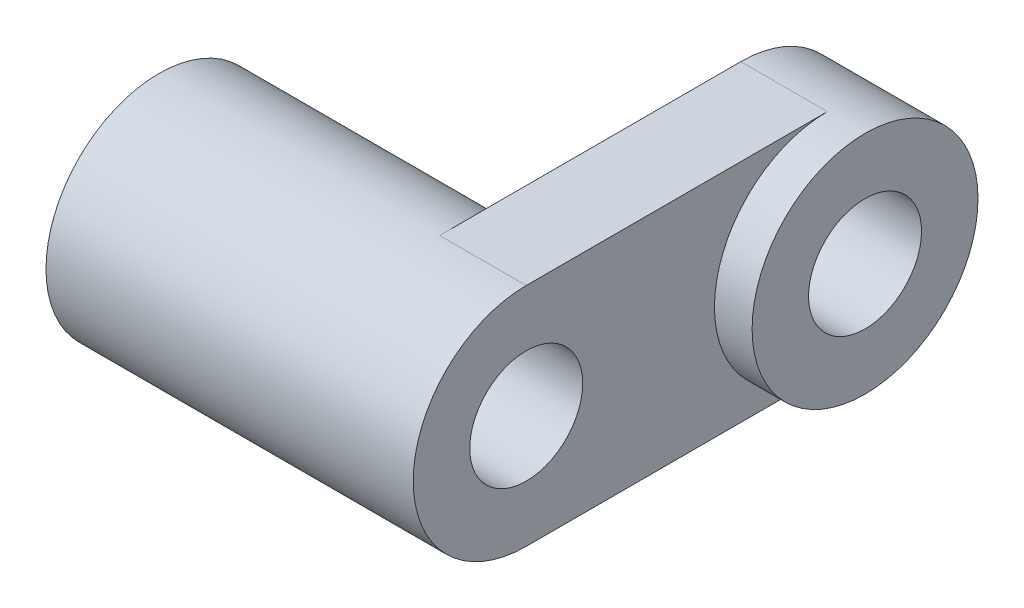
SolidWorks part; units mm, degrees
ref_plane "Front Plane" through (0, 0, 0) normal (0, 0, 1) x (1, 0, 0)
ref_plane "Top Plane" through (0, 0, 0) normal (0, 1, 0) x (1, 0, 0)
ref_plane "Right Plane" through (0, 0, 0) normal (1, 0, 0) x (0, 0, -1)
sketch "Sketch1" plane through (0, 0, 0) normal (1, 0, 0) x (0, 0, -1)
  line L0 (0, 0) -> (8, 0) construction
  line L1 (0, 3) -> (8, 3)
  line L2 (0, -3) -> (8, -3)
  arc A0 (0, 3) -> (0, -3) centre (0, 0) ccw
  arc A1 (8, -3) -> (8, 3) centre (8, 0) ccw
  circle A2 centre (0, 0) radius 1.5
  circle A3 centre (8, 0) radius 1.5
  point P3 (4, 0)
  dimension "D1" = 3
  dimension "D2" = 6
  dimension "D3" = 14
extrude "Boss-Extrude1" add sketch "Sketch1" along normal blind 2.3
sketch "Sketch2" plane through (0, 0, 0) normal (-1, 0, 0) x (0, 0, 1)
  arc A0 (0, -3) -> (0, 3) centre (0, 0) ccw construction
  circle A1 centre (0, 0) radius 3
  circle A2 centre (0, 0) radius 1.5 construction
  circle A3 centre (0, 0) radius 1.5
extrude "Boss-Extrude2" add sketch "Sketch2" along normal offset from surface (7.455 mm away) 9.755 up to face at (2.3, 0, -1.5) offset beyond the face yes
sketch "Sketch3" plane through (2.3, 0, 0) normal (1, 0, 0) x (0, 0, -1)
  arc A0 (8, -3) -> (8, 3) centre (8, 0) ccw construction
  circle A1 centre (8, 0) radius 3
  circle A2 centre (8, 0) radius 1.5 construction
  circle A3 centre (8, 0) radius 1.5
extrude "Boss-Extrude3" add sketch "Sketch3" along normal blind 1
